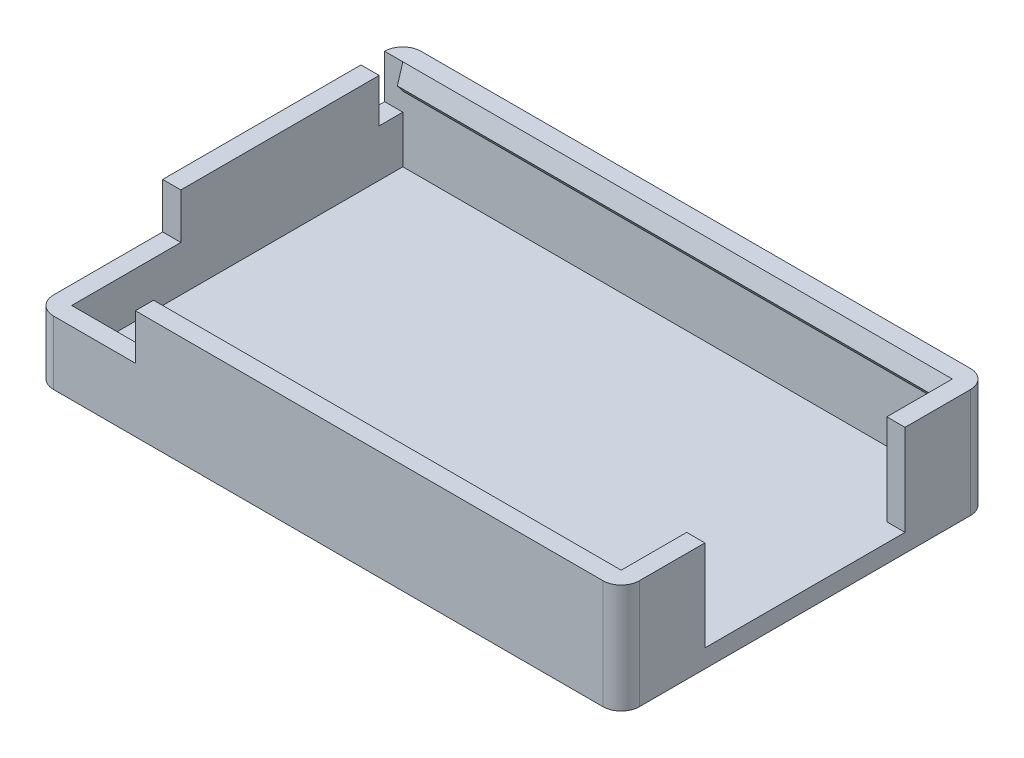
SolidWorks part; units mm, degrees
ref_plane "Front Plane" through (0, 0, 0) normal (0, 0, 1) x (1, 0, 0)
ref_plane "Top Plane" through (0, 0, 0) normal (0, 1, 0) x (1, 0, 0)
ref_plane "Right Plane" through (0, 0, 0) normal (1, 0, 0) x (0, 0, -1)
sketch "Sketch1" plane through (0, 0, 0) normal (0, 1, 0) x (1, 0, 0)
  line L1 (-16.1, -10.1) -> (16.1, -10.1)
  line L2 (-16.1, -10.1) -> (-16.1, 10.1)
  line L3 (-16.1, 10.1) -> (16.1, 10.1)
  line L4 (16.1, -10.1) -> (16.1, 10.1)
  line L5 (-16.1, -10.1) -> (16.1, 10.1) construction
  line L6 (-16.1, 10.1) -> (16.1, -10.1) construction
  point P0 (0, 0)
  dimension "D1" = 20.2
  dimension "D2" = 32.2
extrude "Boss-Extrude1" add sketch "Sketch1" along normal blind 1
sketch "Sketch2" plane through (0, 1, 0) normal (0, 1, 0) x (1, 0, 0)
  line L0 (-16.1, -10.1) -> (16.1, -10.1) construction
  line L1 (-16.1, -10.1) -> (16.1, -10.1)
  line L3 (-16.1, 10.1) -> (16.1, 10.1)
  line L4 (16.1, -10.1) -> (16.1, -5.5)
  line L5 (-16.1, 10.1) -> (-16.1, -10.1)
  line L7 (-15.1, -9.1) -> (15.1, -9.1)
  line L8 (-15.1, -9.1) -> (-15.1, 9.1)
  line L9 (-15.1, 9.1) -> (15.1, 9.1)
  line L10 (15.1, -9.1) -> (15.1, -5.5)
  line L13 (-16.1, 10.1) -> (-16.1, -10.1) construction
  line L14 (15.1, -5.5) -> (16.1, -5.5)
  line L15 (15.1, 5.5) -> (16.1, 5.5)
  line L16 (16.1, 5.5) -> (16.1, 10.1)
  line L17 (15.1, 5.5) -> (15.1, 9.1)
  point P0 (0, 0)
  point P5 (0, 0)
  point P8 (0, 0)
  point P15 (0, 0)
  point P24 (0, 0)
  dimension "D1" = 1
  dimension "D2" = 1
  dimension "D3" = 11
  dimension "D4" = 5.5
  dimension "D5" = 1
  dimension "D6" = 1
extrude "Boss-Extrude2" add sketch "Sketch2" along normal blind 2.5
sketch "Sketch3" plane through (0, 3.5, 0) normal (0, 1, 0) x (1, 0, 0)
  line L0 (-10.6, -9.1) -> (-10.6, -10.1)
  line L1 (-16.1, -3.1) -> (-15.1, -3.1)
  line L12 (16.1, 5.5) -> (16.1, 10.1)
  line L13 (16.1, 10.1) -> (-16.1, 10.1)
  line L14 (-16.1, 10.1) -> (-16.1, -10.1)
  line L15 (-16.1, -10.1) -> (16.1, -10.1)
  line L16 (16.1, -10.1) -> (16.1, -5.5)
  line L17 (16.1, -5.5) -> (15.1, -5.5)
  line L18 (15.1, -5.5) -> (15.1, -9.1)
  line L19 (15.1, -9.1) -> (-15.1, -9.1)
  line L20 (-15.1, -9.1) -> (-15.1, 9.1)
  line L21 (-15.1, 9.1) -> (15.1, 9.1)
  line L22 (15.1, 9.1) -> (15.1, 5.5)
  line L23 (15.1, 5.5) -> (16.1, 5.5)
  line L24 (16.1, 5.5) -> (16.1, 10.1)
  line L25 (16.1, 10.1) -> (-16.1, 10.1)
  line L26 (-16.1, 10.1) -> (-16.1, -3.1)
  line L27 (-10.6, -10.1) -> (16.1, -10.1)
  line L29 (16.1, -5.5) -> (15.1, -5.5)
  line L30 (15.1, -5.5) -> (15.1, -9.1)
  line L31 (15.1, -9.1) -> (-10.6, -9.1)
  line L32 (-15.1, -3.1) -> (-15.1, 9.1)
  line L33 (-15.1, 9.1) -> (15.1, 9.1)
  line L34 (15.1, 9.1) -> (15.1, 5.5)
  line L35 (15.1, 5.5) -> (16.1, 5.5)
  line L39 (16.1, -10.1) -> (16.1, -5.5)
  dimension "D2" = 6
  dimension "D3" = 4.5
  dimension "D1" = 0
extrude "Boss-Extrude3" add sketch "Sketch3" along normal blind 2.5
sketch "Sketch4" plane through (0, 0, 0) normal (1, 0, 0) x (0, 0, -1)
  line L0 (-9.1, 6) -> (-8.8, 5)
  line L1 (-9.1, 6) -> (-9.1, 3.5) construction
  line L3 (-9.1, 3.5) -> (-9.1, 1) construction
  line L4 (-9.1, 5) -> (-9.1, 6)
  line L5 (0, 55) -> (0, -55) construction
  line L6 (-8.8, 5) -> (-9.1, 4.6)
  line L7 (-9.1, 4.6) -> (-9.1, 5)
  line L8 (9.1, 4.6) -> (9.1, 5)
  line L9 (8.8, 5) -> (9.1, 4.6)
  line L10 (9.1, 5) -> (9.1, 6)
  line L11 (9.1, 6) -> (8.8, 5)
  dimension "D1" = 0.4
  dimension "D2" = 0
  dimension "D3" = 0.3
  dimension "D4" = 1
extrude "Boss-Extrude4" add sketch "Sketch4" along normal up to surface and the other way up to surface up to face at (15.1, 3.5, -7.3) other way up to face at (-10.6, 4.75, 9.6)
sketch "Sketch5" plane through (-10.6, 0, 0) normal (-1, 0, 0) x (0, 0, 1)
  line L3 (-9.1, 4.6) -> (-8.8, 5)
  line L4 (-8.8, 5) -> (-9.1, 6)
  line L5 (-9.1, 6) -> (-9.1, 4.6)
  line L6 (-9.1, 4.6) -> (-8.8, 5)
  line L7 (-8.8, 5) -> (-9.1, 6)
  line L10 (-9.1, 6) -> (-9.1, 4.6)
  dimension "D1" = 0
extrude "Boss-Extrude5" add sketch "Sketch5" along normal up to surface (4.5 mm away) up to face at (-15.1, 3.5, 1.0333)
fillet "Fillet1" radius 1 4 edges at (-16.1, 1.75, 10.1) (-16.1, 3, -10.1) (16.1, 3, 10.1) (16.1, 3, -10.1)
sketch "Sketch6" plane through (-15.1, 0, 0) normal (-1, 0, 0) x (0, 0, 1)
  line L5 (-9.1, 6) -> (3.1, 6) construction
  line L15 (-9.1, 6) -> (-9.1, 0) construction
  line L24 (-9.1, 3.6) -> (-9.1, 6)
  line L26 (-7.8, 3.6) -> (-9.1, 3.6)
  line L27 (-7.8, 6) -> (-7.8, 3.6)
  line L28 (-9.1, 6) -> (-7.8, 6)
  dimension "D1" = 1.3
  dimension "D2" = 2.4
extrude "Cut-Extrude1" cut sketch "Sketch6" along normal up to surface (1 mm away) up to face at (-16.1, 3.1667, 1.0333)
